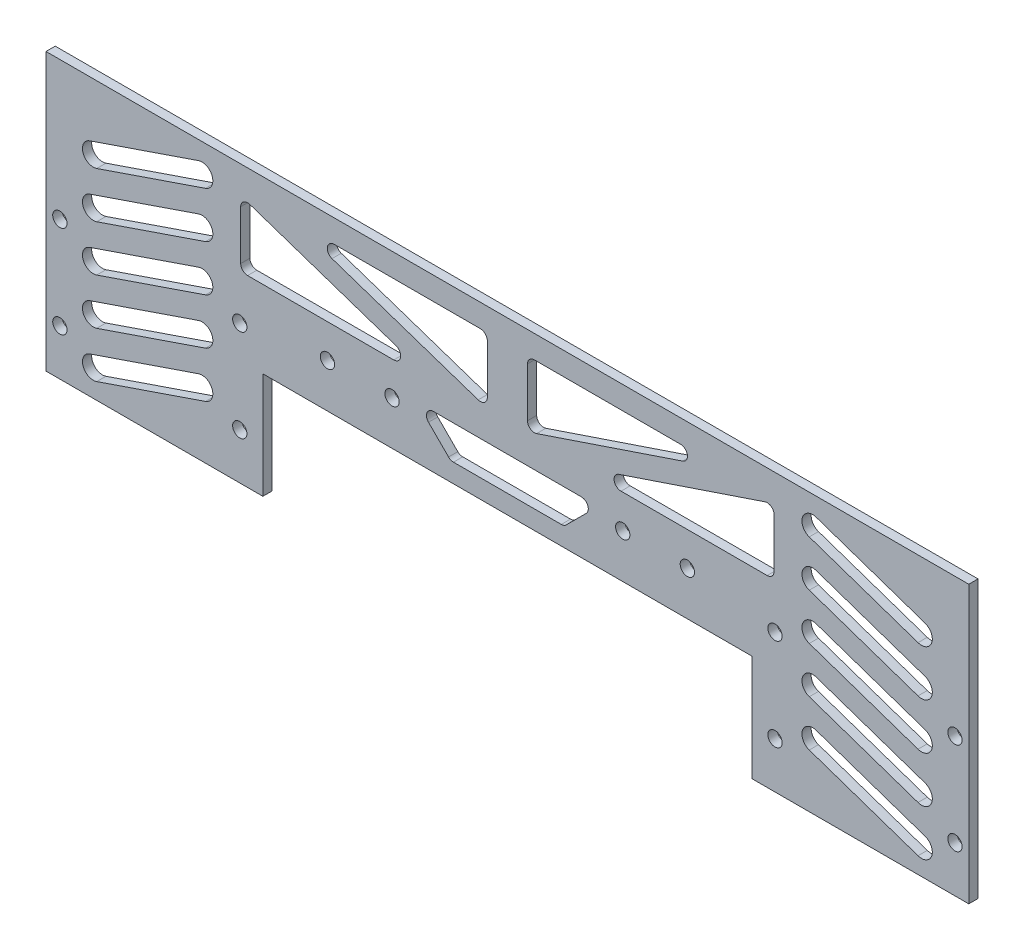
SolidWorks part; units mm, degrees
material "Thornel Mat VMA"
ref_plane "前视基准面" through (0, 0, 0) normal (0, 0, 1) x (1, 0, 0)
ref_plane "上视基准面" through (0, 0, 0) normal (0, 1, 0) x (1, 0, 0)
ref_plane "右视基准面" through (0, 0, 0) normal (1, 0, 0) x (0, 0, -1)
sketch "草图1" plane through (0, 0, 0) normal (0, 0, 1) x (1, 0, 0)
  line L1 (69.1181, 5.8229) -> (69.1181, -30.1771)
  line L2 (69.1181, -30.1771) -> (22.1181, -30.1771)
  line L3 (22.1181, -30.1771) -> (22.1181, -7.1771)
  line L4 (22.1181, -7.1771) -> (-83.8819, -7.1771)
  line L5 (-83.8819, -7.1771) -> (-83.8819, -30.1771)
  line L6 (-83.8819, -30.1771) -> (-130.8819, -30.1771)
  line L7 (-130.8819, -30.1771) -> (-130.8819, 5.8229)
  line L9 (-130.8819, 5.8229) -> (-130.8819, 29.8229)
  line L10 (-130.8819, 29.8229) -> (69.1181, 29.8229)
  line L11 (69.1181, 29.8229) -> (69.1181, 5.8229)
  line L12 (-30.8819, 79.0397) -> (-30.8819, -86.7859) construction
  line L13 (-97.0667, 23.6366) -> (-120.6372, 15.5757) construction
  line L14 (-96.3083, 21.419) -> (-119.8788, 13.3581)
  line L15 (-97.8251, 25.8541) -> (-121.3956, 17.7932)
  line L16 (-97.0667, 13.6366) -> (-120.6372, 5.5757) construction
  line L17 (-96.3083, 11.419) -> (-119.8788, 3.3581)
  line L18 (-97.8251, 15.8541) -> (-121.3956, 7.7932)
  line L19 (-97.0667, 3.6366) -> (-120.6372, -4.4243) construction
  line L20 (-96.3083, 1.419) -> (-119.8788, -6.6419)
  line L21 (-97.8251, 5.8541) -> (-121.3956, -2.2068)
  line L22 (-97.0667, -6.3634) -> (-120.6372, -14.4243) construction
  line L23 (-96.3083, -8.581) -> (-119.8788, -16.6419)
  line L24 (-97.8251, -4.1459) -> (-121.3956, -12.2068)
  line L25 (-97.0667, -16.3634) -> (-120.6372, -24.4243) construction
  line L26 (-96.3083, -18.581) -> (-119.8788, -26.6419)
  line L27 (-97.8251, -14.1459) -> (-121.3956, -22.2068)
  line L28 (35.3028, -16.3634) -> (58.8733, -24.4243) construction
  line L29 (34.5444, -18.581) -> (58.1149, -26.6419)
  line L30 (36.0612, -14.1459) -> (59.6317, -22.2068)
  line L31 (35.3028, -6.3634) -> (58.8733, -14.4243) construction
  line L32 (34.5444, -8.581) -> (58.1149, -16.6419)
  line L33 (36.0612, -4.1459) -> (59.6317, -12.2068)
  line L34 (35.3028, 3.6366) -> (58.8733, -4.4243) construction
  line L35 (34.5444, 1.419) -> (58.1149, -6.6419)
  line L36 (36.0612, 5.8541) -> (59.6317, -2.2068)
  line L37 (35.3028, 13.6366) -> (58.8733, 5.5757) construction
  line L38 (34.5444, 11.419) -> (58.1149, 3.3581)
  line L39 (36.0612, 15.8541) -> (59.6317, 7.7932)
  line L40 (35.3028, 23.6366) -> (58.8733, 15.5757) construction
  line L41 (34.5444, 21.419) -> (58.1149, 13.3581)
  line L42 (36.0612, 25.8541) -> (59.6317, 17.7932)
  line L43 (-86.7071, 23.203) -> (-55.0255, 12.5276)
  line L44 (-68.4157, 24.8592) -> (-36.7341, 24.8592)
  line L45 (-88.6861, 21.7815) -> (-88.6861, 11.1061)
  line L46 (-87.1861, 9.6061) -> (-55.5045, 9.6061)
  line L47 (-35.2341, 23.3592) -> (-35.2341, 12.6838)
  line L48 (26.9222, 21.7815) -> (26.9222, 11.1061)
  line L49 (-88.6861, 9.6061) -> (-35.2341, 24.8592) construction
  line L50 (-68.8946, 21.9378) -> (-37.213, 11.2624)
  line L51 (24.9432, 23.203) -> (-6.7384, 12.5276)
  line L52 (25.4222, 9.6061) -> (-6.2594, 9.6061)
  line L53 (7.1307, 21.9378) -> (-24.5508, 11.2624)
  line L54 (-26.5298, 23.3592) -> (-26.5298, 12.6838)
  line L55 (6.6518, 24.8592) -> (-25.0298, 24.8592)
  line L56 (-14.8468, 4.2377) -> (-46.9171, 4.2377)
  line L57 (-47.9777, 1.6771) -> (-43.6305, -2.6701)
  line L58 (-42.5699, -3.1095) -> (-19.194, -3.1095)
  line L59 (-13.7862, 1.6771) -> (-18.1334, -2.6701)
  circle A0 centre (-127.8819, -0.1771) radius 1.55
  circle A1 centre (-127.8819, -20.1771) radius 1.55
  circle A2 centre (-88.8819, -0.1771) radius 1.55
  circle A3 centre (-88.8819, -20.1771) radius 1.55
  circle A4 centre (27.1181, -0.1771) radius 1.55
  circle A5 centre (27.1181, -20.1771) radius 1.55
  circle A6 centre (66.1181, -0.1771) radius 1.55
  circle A7 centre (66.1181, -20.1771) radius 1.55
  circle A8 centre (-69.8819, 2.3229) radius 1.55
  circle A9 centre (-55.8819, 2.3229) radius 1.55
  circle A10 centre (-5.8819, 2.3229) radius 1.55
  circle A11 centre (8.1181, 2.3229) radius 1.55
  arc A12 (-96.3083, 21.419) -> (-97.8251, 25.8541) centre (-97.0667, 23.6366) ccw
  arc A13 (-121.3956, 17.7932) -> (-119.8788, 13.3581) centre (-120.6372, 15.5757) ccw
  arc A14 (-96.3083, 11.419) -> (-97.8251, 15.8541) centre (-97.0667, 13.6366) ccw
  arc A15 (-121.3956, 7.7932) -> (-119.8788, 3.3581) centre (-120.6372, 5.5757) ccw
  arc A16 (-96.3083, 1.419) -> (-97.8251, 5.8541) centre (-97.0667, 3.6366) ccw
  arc A17 (-121.3956, -2.2068) -> (-119.8788, -6.6419) centre (-120.6372, -4.4243) ccw
  arc A18 (-96.3083, -8.581) -> (-97.8251, -4.1459) centre (-97.0667, -6.3634) ccw
  arc A19 (-121.3956, -12.2068) -> (-119.8788, -16.6419) centre (-120.6372, -14.4243) ccw
  arc A20 (-96.3083, -18.581) -> (-97.8251, -14.1459) centre (-97.0667, -16.3634) ccw
  arc A21 (-121.3956, -22.2068) -> (-119.8788, -26.6419) centre (-120.6372, -24.4243) ccw
  arc A22 (34.5444, -18.581) -> (36.0612, -14.1459) centre (35.3028, -16.3634) cw
  arc A23 (59.6317, -22.2068) -> (58.1149, -26.6419) centre (58.8733, -24.4243) cw
  arc A24 (34.5444, -8.581) -> (36.0612, -4.1459) centre (35.3028, -6.3634) cw
  arc A25 (59.6317, -12.2068) -> (58.1149, -16.6419) centre (58.8733, -14.4243) cw
  arc A26 (34.5444, 1.419) -> (36.0612, 5.8541) centre (35.3028, 3.6366) cw
  arc A27 (59.6317, -2.2068) -> (58.1149, -6.6419) centre (58.8733, -4.4243) cw
  arc A28 (34.5444, 11.419) -> (36.0612, 15.8541) centre (35.3028, 13.6366) cw
  arc A29 (59.6317, 7.7932) -> (58.1149, 3.3581) centre (58.8733, 5.5757) cw
  arc A30 (34.5444, 21.419) -> (36.0612, 25.8541) centre (35.3028, 23.6366) cw
  arc A31 (59.6317, 17.7932) -> (58.1149, 13.3581) centre (58.8733, 15.5757) cw
  arc A32 (-35.2341, 23.3592) -> (-36.7341, 24.8592) centre (-36.7341, 23.3592) ccw
  arc A33 (-35.2341, 12.6838) -> (-37.213, 11.2624) centre (-36.7341, 12.6838) cw
  arc A34 (-68.4157, 24.8592) -> (-68.8946, 21.9378) centre (-68.4157, 23.3592) ccw
  arc A35 (-86.7071, 23.203) -> (-88.6861, 21.7815) centre (-87.1861, 21.7815) ccw
  arc A36 (-88.6861, 11.1061) -> (-87.1861, 9.6061) centre (-87.1861, 11.1061) ccw
  arc A37 (-55.5045, 9.6061) -> (-55.0255, 12.5276) centre (-55.5045, 11.1061) ccw
  arc A38 (24.9432, 23.203) -> (26.9222, 21.7815) centre (25.4222, 21.7815) cw
  arc A39 (26.9222, 11.1061) -> (25.4222, 9.6061) centre (25.4222, 11.1061) cw
  arc A40 (-6.2594, 9.6061) -> (-6.7384, 12.5276) centre (-6.2594, 11.1061) cw
  arc A41 (-26.5298, 12.6838) -> (-24.5508, 11.2624) centre (-25.0298, 12.6838) ccw
  arc A42 (-26.5298, 23.3592) -> (-25.0298, 24.8592) centre (-25.0298, 23.3592) cw
  arc A43 (6.6518, 24.8592) -> (7.1307, 21.9378) centre (6.6518, 23.3592) cw
  arc A44 (-13.7862, 1.6771) -> (-14.8468, 4.2377) centre (-14.8468, 2.7377) ccw
  arc A45 (-18.1334, -2.6701) -> (-19.194, -3.1095) centre (-19.194, -1.6095) cw
  arc A46 (-43.6305, -2.6701) -> (-42.5699, -3.1095) centre (-42.5699, -1.6095) ccw
  arc A47 (-46.9171, 4.2377) -> (-47.9777, 1.6771) centre (-46.9171, 2.7377) ccw
  point P38 (-108.852, 19.6061)
  point P46 (-108.852, 9.6061)
  point P53 (-108.852, -0.3939)
  point P60 (-108.852, -10.3939)
  point P67 (-108.852, -20.3939)
  point P74 (47.0881, -20.3939)
  point P81 (47.0881, -10.3939)
  point P88 (47.0881, -0.3939)
  point P95 (47.0881, 9.6061)
  point P102 (47.0881, 19.6061)
  point P107 (-64.0333, 16.641)
  point P150 (-30.8819, -3.1095)
  point P151 (-30.8819, 4.2377)
  point P153 (-11.2255, 4.2377)
  point P156 (-18.5727, -3.1095)
  point P159 (-43.1912, -3.1095)
  point P162 (-50.5384, 4.2377)
  dimension "D7" = 3
  dimension "D26" = 14
  dimension "D30" = 24
  dimension "D32" = 1.5
  dimension "D33" = 1.5
  dimension "D1" = 47
  dimension "D2" = 47
  dimension "D3" = 106
  dimension "D4" = 36
  dimension "D5" = 30
  dimension "D6" = 9.5
  dimension "D8" = 3
  dimension "D9" = 5
  dimension "D10" = 5
  dimension "D11" = 30
  dimension "D12" = 20
  dimension "D13" = 30
  dimension "D14" = 20
  dimension "D15" = 5
  dimension "D16" = 5
  dimension "D17" = 3
  dimension "D18" = 3
  dimension "D19" = 30
  dimension "D20" = 20
  dimension "D21" = 100
  dimension "D22" = 20
  dimension "D23" = 9.5
  dimension "D24" = 9.5
  dimension "D25" = 9.5
  dimension "D27" = 14
  dimension "D28" = 14
  dimension "D29" = 14
  dimension "D31" = 5
extrude "凸台-拉伸1" add sketch "草图1" along normal blind 2
